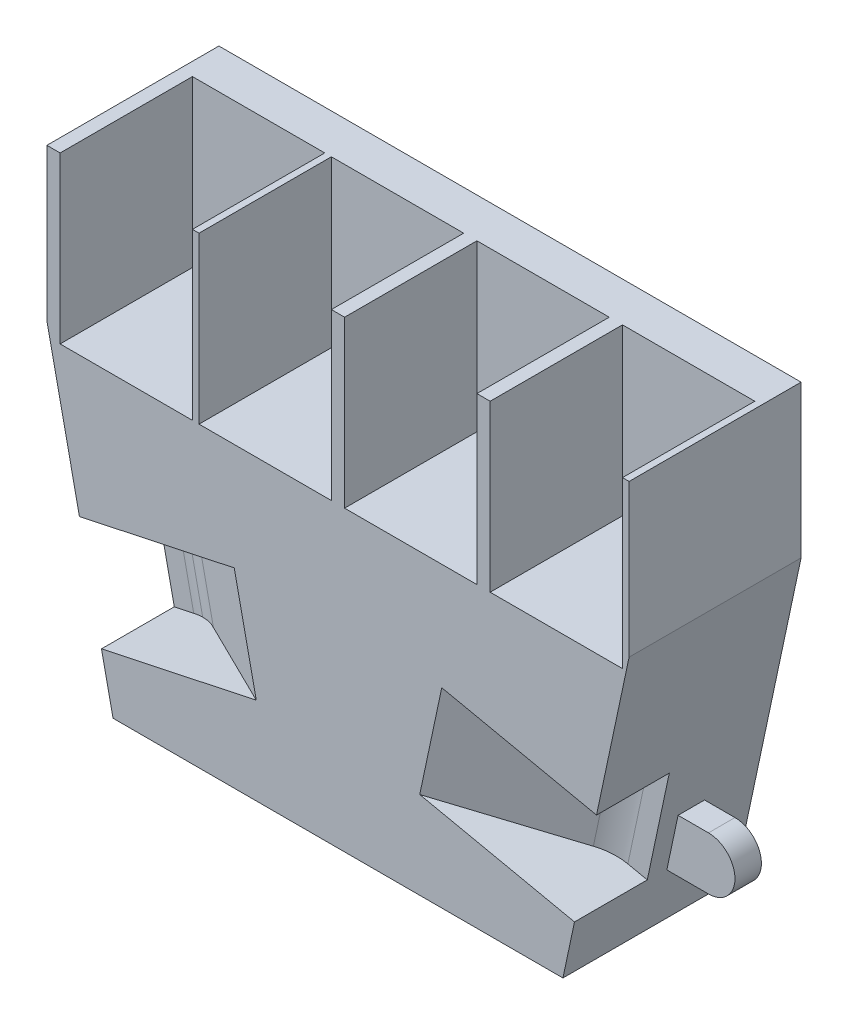
SolidWorks part; units mm, degrees
ref_plane "Front" through (0, 0, 0) normal (0, 0, 1) x (1, 0, 0)
ref_plane "Top" through (0, 0, 0) normal (0, 1, 0) x (1, 0, 0)
ref_plane "Right" through (0, 0, 0) normal (1, 0, 0) x (0, 0, -1)
sketch "草图1" plane through (0, 0, 0) normal (0, 0, 1) x (1, 0, 0)
  line L0 (-34, -24) -> (34, -24)
  line L1 (-44, 46) -> (44, 46)
  line L2 (-44, 46) -> (-44, 23)
  line L4 (44, 46) -> (44, 23)
  line L5 (-66.7553, 0) -> (86.3051, 0) construction
  line L8 (-44, 23) -> (-34, -24)
  line L9 (-44, 23) -> (56.7889, 23) construction
  line L10 (34, -24) -> (44, 23)
  dimension "D1" = 88
  dimension "D3" = 44
  dimension "D4" = 68
  dimension "D5" = 34
  dimension "D6" = 24
extrude "凸台-拉伸1" add sketch "草图1" along normal blind 26
sketch "草图2" plane through (-37.4127, -7.9602, 0) normal (-0.9781, -0.2081, 0) x (0, 0, 1)
  line L0 (13, -16.3989) -> (13, 31.6532) construction
  line L1 (26, -16.3989) -> (0, -16.3989) construction
  line L2 (26, 31.6532) -> (0, 31.6532) construction
  line L3 (0, 0) -> (26, 0)
  line L4 (26, 31.6532) -> (26, -16.3989) construction
sketch "草图3" plane through (0, 0, 0) normal (0, 0, -1) x (-1, 0, 0)
  line L0 (0, -24) -> (0, 47.0389) construction
  line L1 (34, -24) -> (-34, -24) construction
  line L3 (-20, -24) -> (20, -24)
  line L4 (-20, -24) -> (-20, 12)
  line L5 (-20, 12) -> (20, 12)
  line L6 (20, -24) -> (20, 12)
  dimension "D1" = 36
  dimension "D2" = 40
  dimension "D3" = 20
extrude "切除-拉伸4" cut sketch "草图3" against normal blind 20
sketch "草图4" plane through (0, 46, 0) normal (0, 1, 0) x (1, 0, 0)
  line L0 (44, -26) -> (-44, -26) construction
  line L1 (43, -26) -> (23, -26)
  line L2 (43, -26) -> (43, -6)
  line L3 (43, -6) -> (23, -6)
  line L4 (23, -26) -> (23, -6)
  line L5 (44, -26) -> (44, 0) construction
  line L6 (21, -26) -> (1, -26)
  line L7 (21, -26) -> (21, -6)
  line L8 (21, -6) -> (1, -6)
  line L9 (1, -26) -> (1, -6)
  line L10 (-1, -26) -> (-21, -26)
  line L11 (-1, -26) -> (-1, -6)
  line L12 (-1, -6) -> (-21, -6)
  line L13 (-21, -26) -> (-21, -6)
  line L14 (-22, -26) -> (-42, -26)
  line L15 (-22, -26) -> (-22, -6)
  line L16 (-22, -6) -> (-42, -6)
  line L17 (-42, -26) -> (-42, -6)
  dimension "D1" = 20
  dimension "D2" = 21
  dimension "D3" = 20
  dimension "D4" = 20
  dimension "D5" = 20
  dimension "D6" = 2
  dimension "D7" = 2
  dimension "D8" = 20
  dimension "D9" = 20
  dimension "D10" = 20
  dimension "D11" = 21
  dimension "D12" = 20
extrude "切除-拉伸5" cut sketch "草图4" against normal blind 25
sketch3d "3D草图5"
  line L0 (-37.3866, -7.9546, 26.004) -> (-19.9225, -4.2388, 26.004) construction
  line L1 (-37.4127, -7.9602, 0) -> (-37.4127, -7.9602, 26) construction
  line L2 (-37.3866, -7.9546, 26.004) -> (-37.4127, -7.9602, 12.8891) construction
  line L3 (-26.6334, -5.6667, 23.004) -> (-26.6334, -5.6667, 31.004)
  line L4 (-26.6334, -5.6667, 31.004) -> (-34.4583, -7.3315, 31.004)
  arc A0 (-26.6334, -5.6667, 23.004) -> (-34.4583, -7.3315, 31.004) centre (-34.4583, -7.3315, 23.004) ccw
  point P2 (-36.1231, 0.4933, 23.004)
  dimension "D1" = 3
  dimension "D2" = 3
extrude "切除-拉伸3" cut sketch "3D草图5" along direction (0.2081, -0.9781, 0) on the side against the normal mid plane 16
sketch "草图6" plane through (37.4127, -7.9602, 0) normal (0.9781, -0.2081, 0) x (0, 0, -1)
  line L0 (0, 0) -> (-26, 0)
  line L1 (-26, -16.3989) -> (-26, 31.6532) construction
sketch3d "3D草图6"
  line L0 (37.4127, -7.9602, 0) -> (37.4127, -7.9602, 26) construction
  line L2 (37.4127, -7.9602, 26) -> (26.6536, -5.671, 25.9966) construction
  line L3 (34.4784, -7.3358, 14.9991) -> (44.8243, -9.5371, 14.9991)
  line L4 (34.4784, -7.3358, 29) -> (44.8243, -9.5371, 29)
  line L5 (44.8243, -9.5371, 29) -> (44.8243, -9.5371, 14.9991)
  line L6 (26.6536, -5.671, 22.9991) -> (26.6536, -5.671, 29)
  line L7 (26.6536, -5.671, 29) -> (34.4784, -7.3358, 29)
  arc A0 (34.4784, -7.3358, 14.9991) -> (26.6536, -5.671, 22.9991) centre (34.4784, -7.3358, 22.9991) ccw
  point P2 (36.1433, 0.489, 22.9991)
  dimension "D1" = 3
  dimension "D2" = 3
extrude "切除-拉伸6" cut sketch "3D草图6" along direction (0.2081, 0.9781, 0) on the side against the normal mid plane 16
sketch "草图7" plane through (-1.6649, 7.8248, 0) normal (0.2081, -0.9781, 0) x (0.9781, 0.2081, 0)
  line L0 (-38.2502, 0) -> (-38.2502, 26) construction
  line L1 (-38.2502, 26) -> (28.261, 26) construction
  line L2 (-38.2502, 26) -> (-29.5933, 17.3431) construction
  line L3 (-24.5567, 20) -> (-31.2008, 16.1005)
  line L4 (-24.5567, 20) -> (-10.0872, 28.4922)
  line L5 (-10.0872, 28.4922) -> (-33.6713, 30.8426)
  line L6 (-35.2502, 15) -> (-43.2502, 15)
  line L7 (-43.2502, 15) -> (-43.2502, 23)
  arc A0 (-35.2502, 15) -> (-31.2008, 16.1005) centre (-35.2502, 23) ccw
  arc A1 (-33.6713, 30.8426) -> (-43.2502, 23) centre (-35.2502, 23) ccw
  dimension "D3" = 16
  dimension "D1" = 3
  dimension "D2" = 3
extrude "切除-拉伸7" cut sketch "草图7" along normal blind 16
sketch "草图11" plane through (-1.6649, -7.8248, 0) normal (0.2081, 0.9781, 0) x (0.9781, -0.2081, 0)
  line L0 (-28.261, -26) -> (38.2502, -26) construction
  line L1 (38.2502, 0) -> (38.2502, -26) construction
  line L2 (24.5567, -20) -> (31.2008, -16.1005) construction
  line L3 (31.2008, -16.1005) -> (14.3336, -26)
  line L4 (14.3336, -26) -> (32.6666, -30.5713)
  line L5 (35.2502, -15) -> (38.2502, -14.9991)
  line L6 (38.2502, -14.9991) -> (40.4608, -16.9296)
  arc A0 (32.6666, -30.5713) -> (40.4608, -16.9296) centre (35.2502, -23) ccw
  arc A1 (35.2502, -15) -> (31.2008, -16.1005) centre (35.2502, -23) ccw
  dimension "D1" = 3
  dimension "D2" = 3
extrude "切除-拉伸8" cut sketch "草图11" along normal blind 16
sketch "草图12" plane through (0, 0, 0) normal (0, 0, -1) x (-1, 0, 0)
  line L0 (34, -16) -> (36.935, -16)
  line L1 (34, -24) -> (26, -24)
  line L3 (34, -16) -> (30, -16)
  line L4 (26, -24) -> (26, -20)
  line L5 (36.935, -16) -> (34, -24)
  arc A0 (30, -16) -> (26, -20) centre (30, -20) ccw
  dimension "D1" = 8
extrude "切除-拉伸9" cut sketch "草图12" against normal blind 6
sketch "草图13" plane through (0, 0, 0) normal (0, 0, -1) x (-1, 0, 0)
  line L0 (-34, -24) -> (-34, 26.9948) construction
  line L1 (-20, -24) -> (-34, -24) construction
  line L2 (-34, -8) -> (-42, -8)
  line L3 (-34, -8) -> (-34, -16)
  line L4 (-34, -16) -> (-42, -16)
  arc A0 (-42, -8) -> (-42, -16) centre (-42, -12) ccw
  dimension "D1" = 8
  dimension "D2" = 8
extrude "凸台-拉伸2" add sketch "草图13" against normal blind 12
sketch "草图14" plane through (0, 0, 0) normal (0, 0, -1) x (-1, 0, 0)
  line L0 (-37.4043, -8) -> (-35.7021, -16)
  line L1 (-35.7021, -16) -> (-61.4383, -16)
  line L2 (-61.4383, -16) -> (-61.4383, -8)
  line L3 (-61.4383, -8) -> (-37.4043, -8)
extrude "切除-拉伸10" cut sketch "草图14" against normal blind 8
